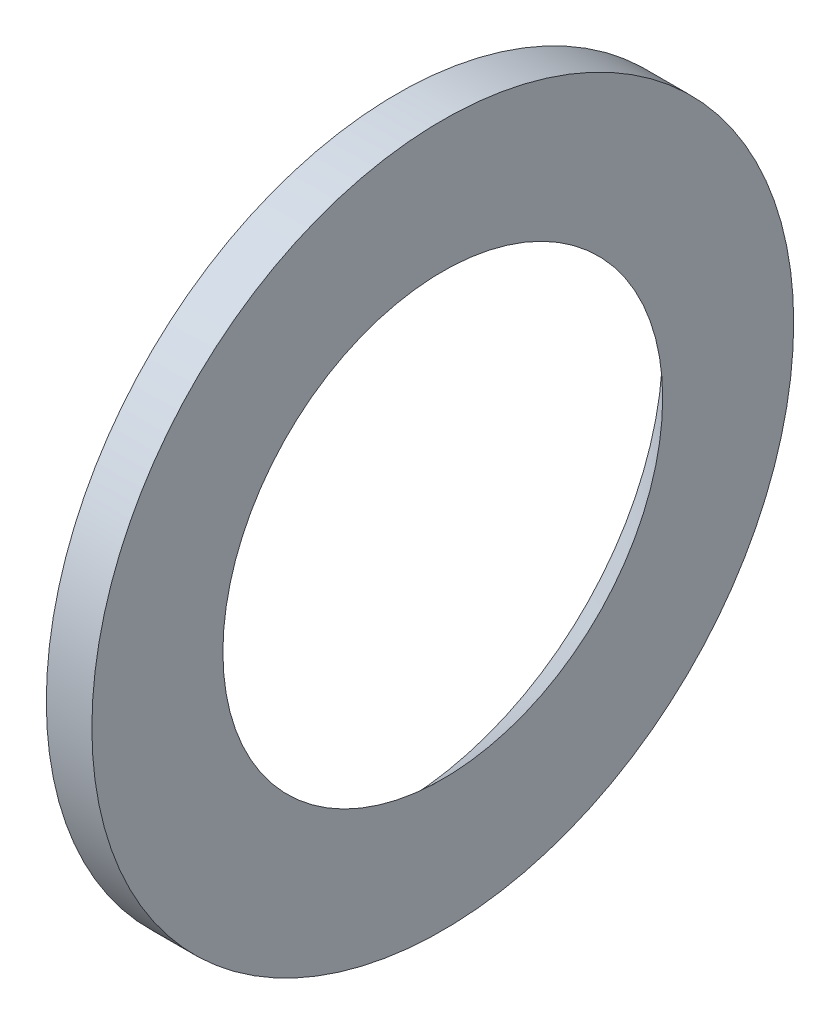
SolidWorks part; units mm, degrees
material "5052-H32"
ref_plane "Přední rovina" through (0, 0, 0) normal (0, 0, 1) x (1, 0, 0)
ref_plane "Horní rovina" through (0, 0, 0) normal (0, 1, 0) x (1, 0, 0)
ref_plane "Pravá rovina" through (0, 0, 0) normal (1, 0, 0) x (0, 0, -1)
sketch "Skica2" plane through (0, 0, 0) normal (0, 0, 1) x (1, 0, 0)
  line L0 (-324.05, -15.4) -> (-322.05, -15.4) construction
  line L1 (-324.05, -11.65) -> (-324.05, -15.4) construction
  line L2 (-322.05, -15.4) -> (-322.05, -9.65) construction
  line L3 (-322.05, -9.65) -> (-324.05, -11.65) construction
  line L4 (-324.05, -15.4) -> (-322.05, -15.4)
  line L5 (-324.05, -11.65) -> (-324.05, -15.4)
  line L6 (-322.05, -15.4) -> (-322.05, -9.65)
  line L7 (-322.05, -9.65) -> (-324.05, -11.65)
  line L8 (-67.4823, 0) -> (-363.0393, 0) construction
  line L9 (-67.4823, 0) -> (-353.9165, 0) construction
revolve "Rotovat2" add sketch "Skica2" angle 360 about L9
